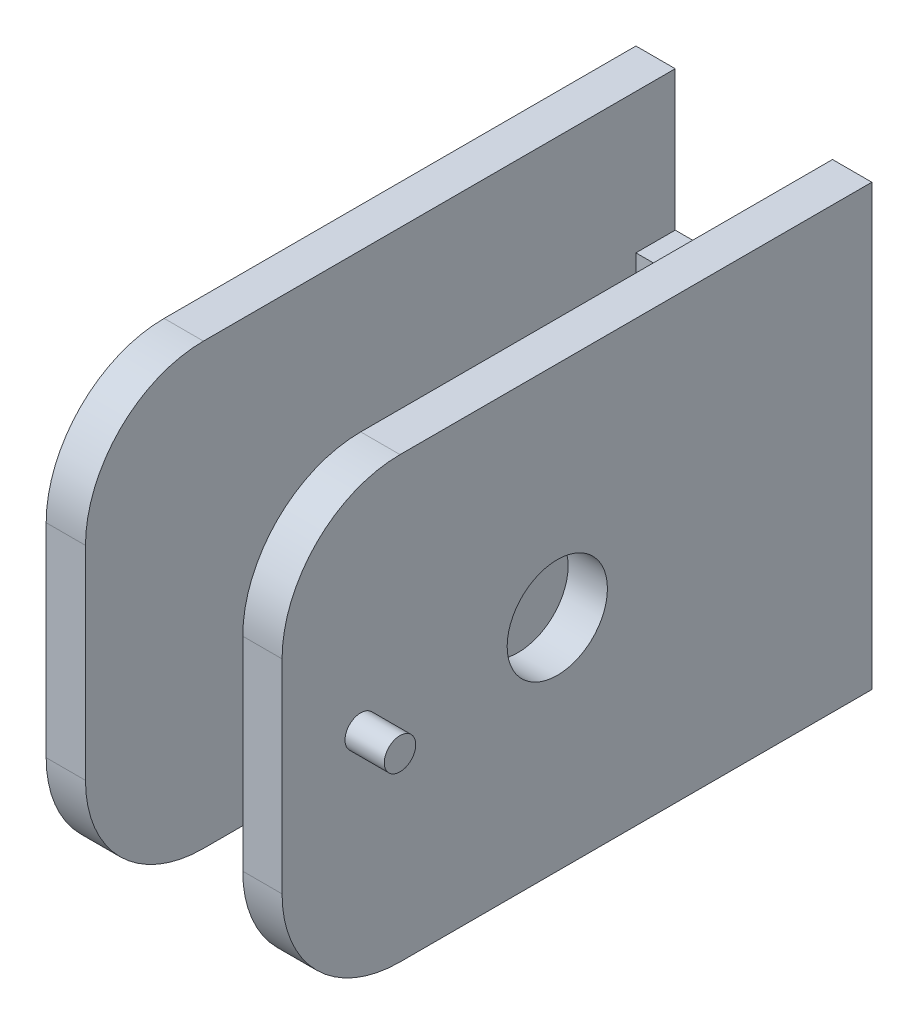
SolidWorks part; units mm, degrees
ref_plane "Front Plane" through (0, 0, 0) normal (0, 0, 1) x (1, 0, 0)
ref_plane "Top Plane" through (0, 0, 0) normal (0, 1, 0) x (1, 0, 0)
ref_plane "Right Plane" through (0, 0, 0) normal (1, 0, 0) x (0, 0, -1)
sketch "Sketch1" plane through (0, 0, 0) normal (0, 1, 0) x (1, 0, 0)
  line L0 (-7.5, -17.5) -> (-7.5, 20)
  line L2 (-5, -17.5) -> (-5, 17.5)
  line L3 (-5, 17.5) -> (5, 17.5)
  line L4 (5, -17.5) -> (5, 17.5)
  line L5 (-5, -17.5) -> (5, 17.5) construction
  line L6 (-5, 17.5) -> (5, -17.5) construction
  line L7 (-7.5, 20) -> (7.5, 20)
  line L8 (7.5, -17.5) -> (7.5, 20)
  line L10 (-5, -17.5) -> (-7.5, -17.5)
  line L11 (5, -17.5) -> (7.5, -17.5)
  line L12 (7.5, -20) -> (7.5, 20) construction
  line L13 (-7.5, -20) -> (7.5, -20) construction
  line L14 (-7.5, -20) -> (-7.5, 20) construction
  line L15 (-5, -17.5) -> (5, -17.5) construction
  point P0 (0, 0)
  dimension "D1" = 10
  dimension "D2" = 35
  dimension "D3" = 2.5
extrude "Boss-Extrude1" add sketch "Sketch1" along normal mid plane 27.94
sketch "Sketch4" plane through (5, 0, 0) normal (-1, 0, 0) x (0, 0, 1)
  line L1 (-20, 13.97) -> (-20, -13.97) construction
  line L2 (0, 13.97) -> (0, -13.97) construction
  line L3 (-20, 13.97) -> (17.5, 13.97) construction
  line L4 (-20, -13.97) -> (17.5, -13.97) construction
  circle A0 centre (0, 0) radius 3.1877
  dimension "D1" = 6.3754
  dimension "D3" = 20
sketch "Sketch5" plane through (7.5, 0, 0) normal (1, 0, 0) x (0, 0, -1)
  line L1 (-17.5, 13.97) -> (-17.5, -13.97) construction
  circle A0 centre (-12.5, 0) radius 1
  point P2 (-17.5, 0)
  dimension "D1" = 2
  dimension "D3" = 5
extrude "Boss-Extrude4" add sketch "Sketch5" along normal blind 2.5
sketch "Sketch6" plane through (0, 0, -20) normal (0, 0, -1) x (-1, 0, 0)
  line L0 (-7.5, -13.97) -> (7.5, -13.97) construction
  line L1 (5, -5.08) -> (-5, -5.08)
  line L2 (5, -5.08) -> (5, -13.97)
  line L3 (5, -13.97) -> (-5, -13.97)
  line L4 (-5, -5.08) -> (-5, -13.97)
  line L5 (5, -5.08) -> (-5, -13.97) construction
  line L6 (5, -13.97) -> (-5, -5.08) construction
  point P0 (0, -9.525)
  dimension "D1" = 10
  dimension "D2" = 8.89
extrude "Cut-Extrude1" cut sketch "Sketch6" against normal up to next (2.5 mm away)
fillet "Fillet1" radius 7.5 4 edges at (-6.25, -13.97, 17.5) (-6.25, 13.97, 17.5) (6.25, -13.97, 17.5) (6.25, 13.97, 17.5)
extrude "Cut-Extrude2" cut sketch "Sketch4" along normal through all both and the other way through all
mirror "Mirror2" about plane through (0, 0, 0) normal (0, 1, 0) of "Cut-Extrude1"
